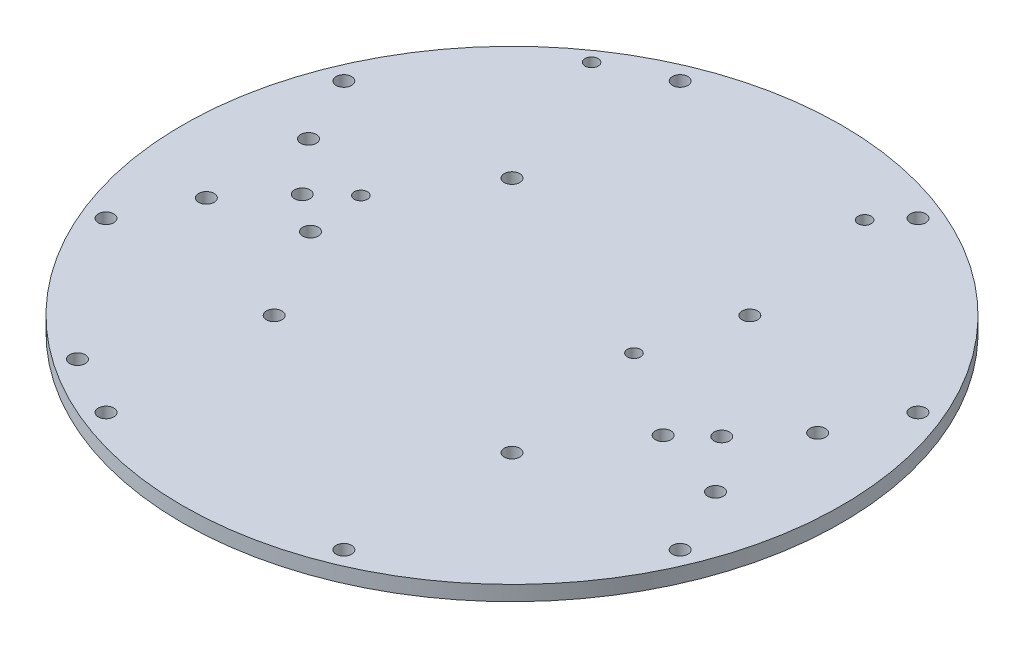
SolidWorks part; units mm, degrees
ref_plane "Front Plane" through (0, 0, 0) normal (0, 0, 1) x (1, 0, 0)
ref_plane "Top Plane" through (0, 0, 0) normal (0, 1, 0) x (1, 0, 0)
ref_plane "Right Plane" through (0, 0, 0) normal (1, 0, 0) x (0, 0, -1)
sketch "Base w/ Motor Mounts" plane through (0, 0, 0) normal (0, 1, 0) x (1, 0, 0)
  line L0 (0, 70) -> (0, -70) construction
  line L1 (0, 0) -> (70, 0) construction
  circle A0 centre (0, 0) radius 70
  circle A1 centre (44.55, 0) radius 1.651
  circle A2 centre (54.075, 10.85) radius 1.651
  circle A3 centre (54.075, -10.85) radius 1.651
  circle A4 centre (-54.075, -10.85) radius 1.651
  circle A5 centre (-54.075, 10.85) radius 1.651
  circle A6 centre (-44.55, 0) radius 1.651
  dimension "D1" = 3.302
  dimension "D6" = 140
  dimension "D2" = 21.7
  dimension "D3" = 10.85
  dimension "D4" = 15.925
  dimension "D5" = 9.525
sketch "Standoffs (top / bottom)" plane through (0, 0, 0) normal (0, 1, 0) x (1, 0, 0)
  line L0 (0, 0) -> (64.6716, 26.7878) construction
  line L1 (0, 0) -> (49.4975, 49.4975) construction
  line L2 (0, 0) -> (26.7878, 64.6716) construction
  line L3 (0, 0) -> (70, 0) construction
  line L4 (-70, 0) -> (70, 0) construction
  line L5 (0, 0) -> (64.6716, -26.7878) construction
  line L6 (0, 0) -> (49.4975, -49.4975) construction
  line L7 (0, 0) -> (26.7878, -64.6716) construction
  line L8 (0, 70) -> (0, -70) construction
  line L9 (0, 0) -> (-26.7878, -64.6716) construction
  line L10 (0, 0) -> (-49.4975, -49.4975) construction
  line L11 (0, 0) -> (-64.6716, -26.7878) construction
  line L12 (0, 0) -> (-26.7878, 64.6716) construction
  line L13 (0, 0) -> (-49.4975, 49.4975) construction
  line L14 (0, 0) -> (-64.6716, 26.7878) construction
  line L15 (25.2571, 60.976) -> (25.2571, 25.2571) construction
  circle A0 centre (0, 0) radius 70 construction
  circle A1 centre (25.2571, 60.976) radius 1.65
  circle A3 centre (60.976, 25.2571) radius 1.65
  circle A4 centre (25.2571, 25.2571) radius 1.65
  circle A5 centre (25.2571, -25.2571) radius 1.65
  circle A6 centre (60.976, -25.2571) radius 1.65
  circle A7 centre (25.2571, -60.976) radius 1.65
  circle A8 centre (-25.2571, -60.976) radius 1.65
  circle A9 centre (-60.976, -25.2571) radius 1.65
  circle A10 centre (-25.2571, -25.2571) radius 1.65
  circle A11 centre (-25.2571, 25.2571) radius 1.65
  circle A12 centre (-60.976, 25.2571) radius 1.65
  circle A13 centre (-25.2571, 60.976) radius 1.65
  point P50 (24.5467, 24.5467)
  dimension "D4" = 3.3
  dimension "D1" = 22.5
  dimension "D2" = 22.5
  dimension "D3" = 22.5
  dimension "D5" = 4
  dimension "D7" = 4
  dimension "D6" = 35.7189
sketch "Pi and Mega Standoffs" plane through (0, 0, 0) normal (0, 1, 0) x (1, 0, 0)
  line L0 (0, 70) -> (0, -70) construction
  line L1 (-38.1, 55) -> (19.9, 55) construction
  line L2 (-38.1, 55) -> (-38.1, 6) construction
  line L3 (-38.1, 6) -> (19.9, 6) construction
  line L4 (19.9, 55) -> (19.9, 6) construction
  line L5 (-38.1, 55) -> (19.9, 6) construction
  line L6 (-38.1, 6) -> (19.9, 55) construction
  line L7 (0, 0) -> (70, 0) construction
  line L8 (-38.1, -6) -> (38.1, -6) construction
  line L9 (-38.1, -6) -> (-38.1, -54.2) construction
  line L10 (-38.1, -54.2) -> (38.1, -54.2) construction
  line L11 (38.1, -6) -> (38.1, -54.2) construction
  line L12 (-38.1, -6) -> (38.1, -54.2) construction
  line L13 (-38.1, -54.2) -> (38.1, -6) construction
  circle A0 centre (-38.1, 55) radius 1.4
  circle A1 centre (19.9, 55) radius 1.4
  circle A2 centre (19.9, 6) radius 1.4
  circle A3 centre (-38.1, 6) radius 1.4
  circle A4 centre (-38.1, -54.2) radius 1.65
  circle A5 centre (-36.8, -6) radius 1.65
  circle A6 centre (38.1, -6) radius 1.65
  point P0 (-10.6204, 31.3097)
  point P11 (0, -30.1)
  point P23 (0, 0)
  point P24 (-10.6204, 31.3097)
  dimension "D3" = 2.8
  dimension "D5" = 3.3
  dimension "D1" = 49
  dimension "D2" = 58
  dimension "D4" = 76.2
  dimension "D6" = 1.3
  dimension "D7" = 74.9
  dimension "D8" = 48.2
  dimension "D9" = 6
  dimension "D10" = 6
extrude "Boss-Extrude1" add sketch "Base w/ Motor Mounts" along normal blind 3.175
extrude "Cut-Extrude2" cut sketch "Standoffs (top / bottom)" along normal blind 3.175
extrude "Cut-Extrude3" cut sketch "Pi and Mega Standoffs" along normal blind 3.175
equation "\"D7@Standoffs (top / bottom)\" = \"D5@Standoffs (top / bottom)\""
equation "\"D10@Pi and Mega Standoffs\"=\"D9@Pi and Mega Standoffs\""
